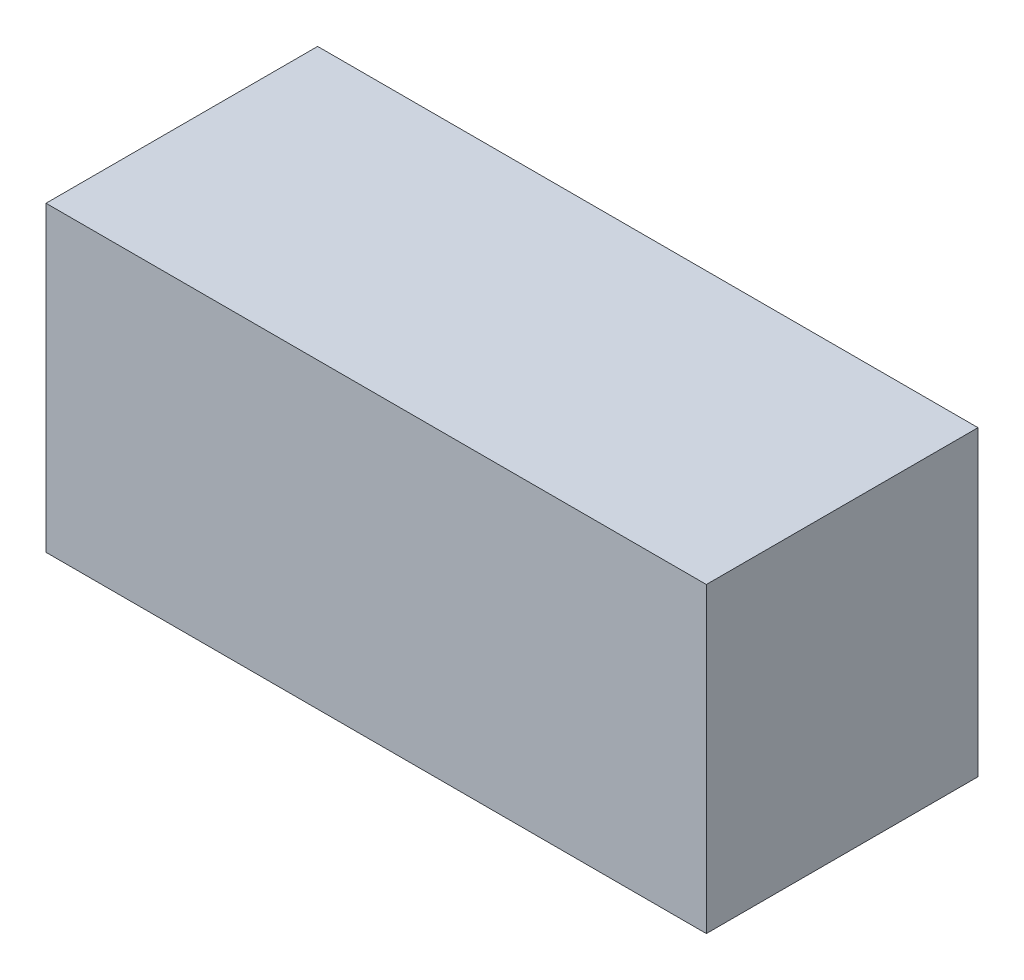
SolidWorks part; units mm, degrees
ref_plane "Front Plane" through (0, 0, 0) normal (0, 0, 1) x (1, 0, 0)
ref_plane "Top Plane" through (0, 0, 0) normal (0, 1, 0) x (1, 0, 0)
ref_plane "Right Plane" through (0, 0, 0) normal (1, 0, 0) x (0, 0, -1)
sketch "Sketch1" plane through (0, 0, 0) normal (0, 0, 1) x (1, 0, 0)
  line L1 (-24.31, -11.13) -> (24.31, -11.13)
  line L2 (-24.31, -11.13) -> (-24.31, 11.13)
  line L3 (-24.31, 11.13) -> (24.31, 11.13)
  line L4 (24.31, -11.13) -> (24.31, 11.13)
  line L5 (-24.31, -11.13) -> (24.31, 11.13) construction
  line L6 (-24.31, 11.13) -> (24.31, -11.13) construction
  point P0 (0, 0)
  dimension "D1" = 48.62
  dimension "D2" = 22.26
extrude "Boss-Extrude1" add sketch "Sketch1" along normal blind 20 contours L3 L4 L1 L2
